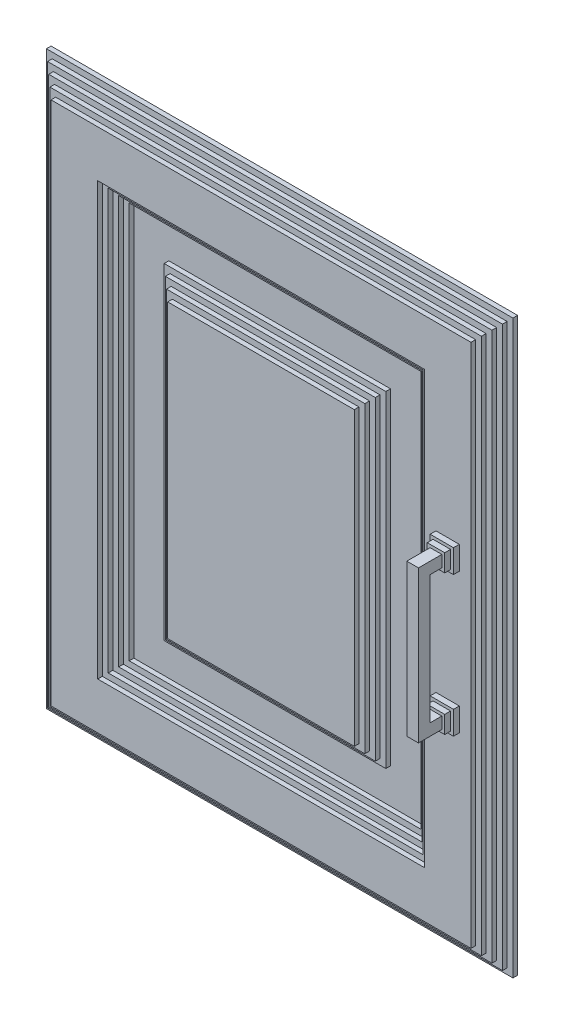
SolidWorks part; units mm, degrees
material "Mahogany"
ref_plane "Front Plane" through (0, 0, 0) normal (0, 0, 1) x (1, 0, 0)
ref_plane "Top Plane" through (0, 0, 0) normal (0, 1, 0) x (1, 0, 0)
ref_plane "Right Plane" through (0, 0, 0) normal (1, 0, 0) x (0, 0, -1)
sketch "Sketch1" plane through (0, 0, 0) normal (0, 0, 1) x (1, 0, 0)
  line L20 (200, 0) -> (200, -20)
  line L21 (200, -20) -> (200, -245)
  line L22 (-200, -245) -> (200, -245)
  line L23 (-200, -20) -> (-200, -245)
  line L24 (-200, 0) -> (-200, -20)
  line L25 (-200, 245) -> (-200, 0)
  line L26 (-200, 245) -> (200, 245)
  line L27 (200, 245) -> (200, 0)
  point P0 (0, 0)
  point P1 (-175, 220)
  point P2 (175, -220)
  point P3 (-175, -220)
  point P4 (175, 220)
extrude "Boss-Extrude2" add sketch "Sketch1" along normal blind 4
sketch "Sketch2" plane through (0, 0, 4) normal (0, 0, 1) x (1, 0, 0)
  line L8 (195, -240) -> (195, 240)
  line L9 (195, 240) -> (-195, 240)
  line L10 (-195, 240) -> (-195, -240)
  line L11 (-195, -240) -> (195, -240)
  line L12 (195, -240) -> (195, 240)
  line L13 (195, 240) -> (-195, 240)
  line L14 (-195, 240) -> (-195, -240)
  line L15 (-195, -240) -> (195, -240)
  dimension "D1" = 5
extrude "Boss-Extrude3" add sketch "Sketch2" along normal blind 4
sketch "Sketch3" plane through (0, 0, 8) normal (0, 0, 1) x (1, 0, 0)
  line L8 (-190, -235) -> (190, -235)
  line L9 (190, -235) -> (190, 235)
  line L10 (190, 235) -> (-190, 235)
  line L11 (-190, 235) -> (-190, -235)
  line L12 (-190, -235) -> (190, -235)
  line L13 (190, -235) -> (190, 235)
  line L14 (190, 235) -> (-190, 235)
  line L15 (-190, 235) -> (-190, -235)
  dimension "D1" = 5
extrude "Boss-Extrude4" add sketch "Sketch3" along normal blind 4
sketch "Sketch4" plane through (0, 0, 12) normal (0, 0, 1) x (1, 0, 0)
  line L8 (-185, 230) -> (-185, -230)
  line L9 (-185, -230) -> (185, -230)
  line L10 (185, -230) -> (185, 230)
  line L11 (185, 230) -> (-185, 230)
  line L12 (-185, 230) -> (-185, -230)
  line L13 (-185, -230) -> (185, -230)
  line L14 (185, -230) -> (185, 230)
  line L15 (185, 230) -> (-185, 230)
  dimension "D1" = 5
extrude "Boss-Extrude5" add sketch "Sketch4" along normal blind 4
sketch "Sketch5" plane through (0, 0, 16) normal (0, 0, 1) x (1, 0, 0)
  line L8 (180, 225) -> (-180, 225)
  line L9 (-180, 225) -> (-180, -225)
  line L10 (-180, -225) -> (180, -225)
  line L11 (180, -225) -> (180, 225)
  line L12 (180, 225) -> (-180, 225)
  line L13 (-180, 225) -> (-180, -225)
  line L14 (-180, -225) -> (180, -225)
  line L15 (180, -225) -> (180, 225)
  dimension "D1" = 5
extrude "Boss-Extrude6" add sketch "Sketch5" along normal blind 4
sketch "Sketch6" plane through (0, 0, 20) normal (0, 0, 1) x (1, 0, 0)
  line L8 (140, -185) -> (140, 185)
  line L9 (140, 185) -> (-140, 185)
  line L10 (-140, 185) -> (-140, -185)
  line L11 (-140, -185) -> (140, -185)
  line L12 (140, -185) -> (140, 185)
  line L13 (140, 185) -> (-140, 185)
  line L14 (-140, 185) -> (-140, -185)
  line L15 (-140, -185) -> (140, -185)
  dimension "D1" = 40
extrude "Cut-Extrude1" cut sketch "Sketch6" against normal blind 4
sketch "Sketch7" plane through (0, 0, 16) normal (0, 0, 1) x (1, 0, 0)
  line L8 (-135, -180) -> (135, -180)
  line L9 (135, -180) -> (135, 180)
  line L10 (135, 180) -> (-135, 180)
  line L11 (-135, 180) -> (-135, -180)
  line L12 (-135, -180) -> (135, -180)
  line L13 (135, -180) -> (135, 180)
  line L14 (135, 180) -> (-135, 180)
  line L15 (-135, 180) -> (-135, -180)
  dimension "D1" = 5
extrude "Cut-Extrude2" cut sketch "Sketch7" against normal blind 4
sketch "Sketch8" plane through (0, 0, 12) normal (0, 0, 1) x (1, 0, 0)
  line L8 (-130, 175) -> (-130, -175)
  line L9 (-130, -175) -> (130, -175)
  line L10 (130, -175) -> (130, 175)
  line L11 (130, 175) -> (-130, 175)
  line L12 (-130, 175) -> (-130, -175)
  line L13 (-130, -175) -> (130, -175)
  line L14 (130, -175) -> (130, 175)
  line L15 (130, 175) -> (-130, 175)
  dimension "D1" = 5
extrude "Cut-Extrude3" cut sketch "Sketch8" against normal blind 4
sketch "Sketch9" plane through (0, 0, 8) normal (0, 0, 1) x (1, 0, 0)
  line L8 (125, 170) -> (-125, 170)
  line L9 (-125, 170) -> (-125, -170)
  line L10 (-125, -170) -> (125, -170)
  line L11 (125, -170) -> (125, 170)
  line L12 (125, 170) -> (-125, 170)
  line L13 (-125, 170) -> (-125, -170)
  line L14 (-125, -170) -> (125, -170)
  line L15 (125, -170) -> (125, 170)
  dimension "D1" = 5
extrude "Cut-Extrude4" cut sketch "Sketch9" against normal blind 4
sketch "Sketch11" plane through (0, 0, 4) normal (0, 0, 1) x (1, 0, 0)
  line L8 (95, -140) -> (95, 140)
  line L9 (95, 140) -> (-95, 140)
  line L10 (-95, 140) -> (-95, -140)
  line L11 (-95, -140) -> (95, -140)
  line L12 (95, -140) -> (95, 140)
  line L13 (95, 140) -> (-95, 140)
  line L14 (-95, 140) -> (-95, -140)
  line L15 (-95, -140) -> (95, -140)
  dimension "D1" = 30
extrude "Boss-Extrude7" add sketch "Sketch11" along normal blind 4
sketch "Sketch12" plane through (0, 0, 8) normal (0, 0, 1) x (1, 0, 0)
  line L8 (-90, -135) -> (90, -135)
  line L9 (90, -135) -> (90, 135)
  line L10 (90, 135) -> (-90, 135)
  line L11 (-90, 135) -> (-90, -135)
  line L12 (-90, -135) -> (90, -135)
  line L13 (90, -135) -> (90, 135)
  line L14 (90, 135) -> (-90, 135)
  line L15 (-90, 135) -> (-90, -135)
  dimension "D1" = 5
extrude "Boss-Extrude8" add sketch "Sketch12" along normal blind 4
sketch "Sketch13" plane through (0, 0, 12) normal (0, 0, 1) x (1, 0, 0)
  line L8 (-85, 130) -> (-85, -130)
  line L9 (-85, -130) -> (85, -130)
  line L10 (85, -130) -> (85, 130)
  line L11 (85, 130) -> (-85, 130)
  line L12 (-85, 130) -> (-85, -130)
  line L13 (-85, -130) -> (85, -130)
  line L14 (85, -130) -> (85, 130)
  line L15 (85, 130) -> (-85, 130)
  dimension "D1" = 5
extrude "Boss-Extrude9" add sketch "Sketch13" along normal blind 4
sketch "Sketch14" plane through (0, 0, 16) normal (0, 0, 1) x (1, 0, 0)
  line L8 (80, 125) -> (-80, 125)
  line L9 (-80, 125) -> (-80, -125)
  line L10 (-80, -125) -> (80, -125)
  line L11 (80, -125) -> (80, 125)
  line L12 (80, 125) -> (-80, 125)
  line L13 (-80, 125) -> (-80, -125)
  line L14 (-80, -125) -> (80, -125)
  line L15 (80, -125) -> (80, 125)
  dimension "D1" = 5
extrude "Boss-Extrude10" add sketch "Sketch14" along normal blind 4
sketch "Sketch15" plane through (0, 0, 20) normal (0, 0, 1) x (1, 0, 0)
  line L0 (-250.7048, 0) -> (237.257, 0) construction
  line L1 (0, 277.7734) -> (0, -276.8061) construction
  line L3 (150, 70) -> (170, 70)
  line L4 (150, 70) -> (150, 50)
  line L5 (150, 50) -> (170, 50)
  line L6 (170, 70) -> (170, 50)
  line L7 (180, -225) -> (180, 225) construction
  line L8 (140, -185) -> (140, 185) construction
  line L9 (150, -50) -> (170, -50)
  line L10 (170, -70) -> (170, -50)
  line L11 (150, -70) -> (170, -70)
  line L12 (150, -70) -> (150, -50)
  dimension "D1" = 50
  dimension "D2" = 20
  dimension "D3" = 20
  dimension "D4" = 10
  dimension "D5" = 10
extrude "Boss-Extrude11" add sketch "Sketch15" along normal blind 5
sketch "Sketch16" plane through (0, 0, 25) normal (0, 0, 1) x (1, 0, 0)
  line L0 (160, 72.9811) -> (160, 48.56) construction
  line L1 (170, 60) -> (150, 60) construction
  line L2 (170, 50) -> (170, 70) construction
  line L3 (150, 70) -> (150, 50) construction
  line L4 (-228.2363, 0) -> (215.6457, 0) construction
  line L5 (167.5, 52.5) -> (152.5, 52.5)
  line L6 (167.5, 52.5) -> (167.5, 67.5)
  line L7 (167.5, 67.5) -> (152.5, 67.5)
  line L8 (152.5, 52.5) -> (152.5, 67.5)
  line L9 (167.5, 52.5) -> (152.5, 67.5) construction
  line L10 (167.5, 67.5) -> (152.5, 52.5) construction
  line L11 (167.5, -67.5) -> (152.5, -67.5)
  line L12 (152.5, -52.5) -> (152.5, -67.5)
  line L13 (167.5, -52.5) -> (152.5, -52.5)
  line L14 (167.5, -52.5) -> (167.5, -67.5)
  point P8 (160, 60)
  dimension "D1" = 15
  dimension "D2" = 15
extrude "Boss-Extrude12" add sketch "Sketch16" along normal blind 5
sketch "Sketch17" plane through (0, 0, 30) normal (0, 0, 1) x (1, 0, 0)
  line L0 (160, 67.5) -> (160, 52.5) construction
  line L1 (167.5, 67.5) -> (152.5, 67.5) construction
  line L2 (152.5, 52.5) -> (167.5, 52.5) construction
  line L3 (152.5, 60) -> (167.5, 60) construction
  line L4 (152.5, 67.5) -> (152.5, 52.5) construction
  line L5 (167.5, 52.5) -> (167.5, 67.5) construction
  line L6 (-224.1377, 0) -> (213.8305, 0) construction
  line L7 (165, 65) -> (155, 65)
  line L8 (165, 65) -> (165, 55)
  line L9 (165, 55) -> (155, 55)
  line L10 (155, 65) -> (155, 55)
  line L11 (165, 65) -> (155, 55) construction
  line L12 (165, 55) -> (155, 65) construction
  line L13 (165, -55) -> (155, -55)
  line L14 (155, -65) -> (155, -55)
  line L15 (165, -65) -> (155, -65)
  line L16 (165, -65) -> (165, -55)
  point P12 (160, 60)
  dimension "D1" = 10
  dimension "D2" = 10
extrude "Boss-Extrude13" add sketch "Sketch17" along normal blind 20
sketch "Sketch18" plane through (0, 55, 0) normal (0, -1, 0) x (1, 0, 0)
  line L0 (165, 50) -> (165, 30) construction
  line L1 (155, 50) -> (165, 50)
  line L2 (155, 50) -> (155, 40)
  line L3 (155, 40) -> (165, 40)
  line L4 (165, 50) -> (165, 40)
extrude "Boss-Extrude14" add sketch "Sketch18" along normal up to next
sketch "Sketch19" plane through (0, 0, 0) normal (0, 0, -1) x (-1, 0, 0)
  line L0 (165, 191.875) -> (165, 101.875)
  line L1 (200, 191.875) -> (200, 141.875)
  line L2 (200, 191.875) -> (165, 191.875)
  line L3 (165, -108.125) -> (165, -198.125)
  line L4 (200, -108.125) -> (200, -158.125)
  line L5 (200, -108.125) -> (165, -108.125)
  line L6 (195, -198.125) -> (195, -158.125)
  line L7 (195, -158.125) -> (200, -158.125)
  line L8 (195, 101.875) -> (195, 141.875)
  line L9 (195, 141.875) -> (200, 141.875)
  line L10 (200, 245) -> (200, -245) construction
  line L11 (-200, 245) -> (200, 245) construction
  arc A0 (165, -198.125) -> (195, -198.125) centre (180, -191.875) ccw
  arc A1 (165, 101.875) -> (195, 101.875) centre (180, 108.125) ccw
  dimension "D3" = 16.25
  dimension "D11" = 216.25
  dimension "D16" = 16.25
  dimension "D17" = 83.75
  dimension "D2" = 35
  dimension "D4" = 5
  dimension "D5" = 40
  dimension "D6" = 30
  dimension "D7" = 83.75
  dimension "D8" = 53.125
  dimension "D9" = 90
  dimension "D10" = 50
  dimension "D12" = 50
  dimension "D13" = 40
  dimension "D14" = 35
  dimension "D15" = 30
  dimension "D18" = 90
  dimension "D19" = 83.75
extrude "Cut-Extrude6" cut sketch "Sketch19" against normal blind 3
